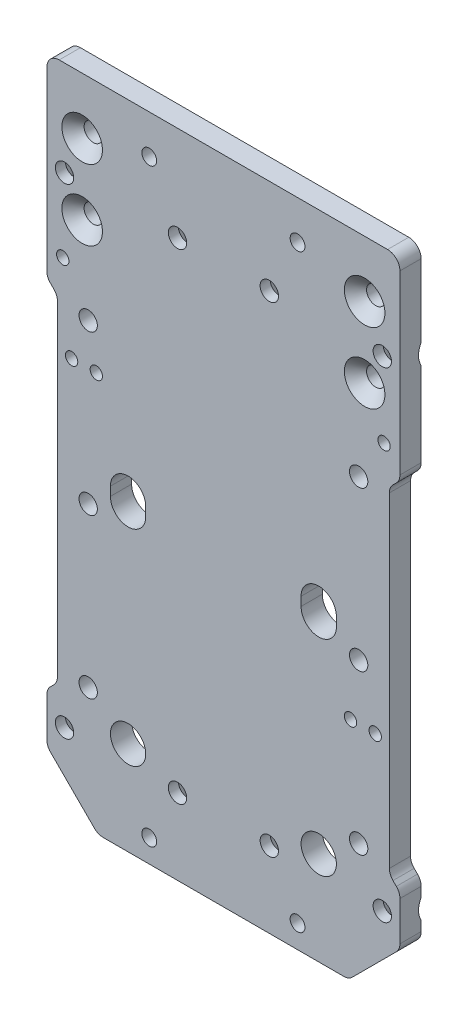
SolidWorks part; units mm, degrees
material "Polycarbonate (PC)"
ref_plane "Front Plane" through (0, 0, 0) normal (0, 0, 1) x (1, 0, 0)
ref_plane "Top Plane" through (0, 0, 0) normal (0, 1, 0) x (1, 0, 0)
ref_plane "Right Plane" through (0, 0, 0) normal (1, 0, 0) x (0, 0, -1)
sketch "Sketch1" plane through (0, 0, 0) normal (0, 0, 1) x (1, 0, 0)
  line L0 (-50, 0) -> (-35.5, -14.5)
  line L1 (-50, 0) -> (50, 0)
  line L2 (-50, 0) -> (-50, 170)
  line L3 (-50, 170) -> (50, 170)
  line L4 (50, 0) -> (50, 170)
  line L5 (-35.5, -14.5) -> (35.5, -14.5)
  line L6 (35.5, -14.5) -> (50, 0)
  line L7 (0, 0) -> (0, 178.5984) construction
  point P4 (0, 0)
  point P8 (0, -14.5)
  dimension "D1" = 100
  dimension "D3" = 14.5
  dimension "D4" = 71
  dimension "D5" = 184.5
extrude "Body" add sketch "Sketch1" along normal mid plane 6 contours L1 L4 L3 L2 | L5 L6 L1 L0 | L1 L7 L3 L2
sketch "Sketch6" plane through (0, 0, 3) normal (0, 0, 1) x (1, 0, 0)
  line L0 (-50, 115) -> (-47, 112)
  line L1 (0, 0) -> (0, 25.1631) construction
  line L2 (-47, 112) -> (-47, 17)
  line L3 (-47, 17) -> (-50, 14)
  line L4 (50, 115) -> (47, 112)
  line L5 (-35.5, -14.5) -> (35.5, -14.5) construction
  line L6 (47, 112) -> (47, 17)
  line L7 (47, 17) -> (50, 14)
  line L8 (-50, 115) -> (-50, 14)
  line L9 (50, 115) -> (50, 14)
  line L12 (-50, 0) -> (-50, 170) construction
  line L13 (50, 0) -> (50, 170) construction
  dimension "D1" = 94
  dimension "D2" = 28.5
  dimension "D3" = 45
  dimension "D4" = 129.5
extrude "ReduceSomeWidth" cut sketch "Sketch6" against normal through all
sketch "screwHeadHoleCarriageY" plane through (0, 0, -3) normal (0, 0, -1) x (-1, 0, 0)
  line L0 (0, 0) -> (0, 34.2129) construction
  line L1 (35.5, -14.5) -> (-35.5, -14.5) construction
  line L2 (-27, 70.2) -> (-27, 72.7) construction
  line L3 (-32, 70.2) -> (-32, 72.7)
  line L4 (-22, 70.2) -> (-22, 72.7)
  line L5 (27, 70.2) -> (27, 72.7) construction
  line L6 (22, 70.2) -> (22, 72.7)
  line L7 (32, 70.2) -> (32, 72.7)
  circle A0 centre (-27, 12) radius 5
  circle A1 centre (27, 12) radius 5
  arc A6 (-32, 70.2) -> (-22, 70.2) centre (-27, 70.2) ccw
  arc A7 (-22, 72.7) -> (-32, 72.7) centre (-27, 72.7) ccw
  arc A8 (22, 70.2) -> (32, 70.2) centre (27, 70.2) ccw
  arc A9 (32, 72.7) -> (22, 72.7) centre (27, 72.7) ccw
  point P18 (-27, 71.45)
  point P28 (27, 71.45)
  dimension "D3" = 10
  dimension "D5" = 12.5
  dimension "D1" = 54
  dimension "D2" = 26.5
  dimension "D4" = 84.7
extrude "CutForOtherScrewsHeads" cut sketch "screwHeadHoleCarriageY" against normal through all
fillet "EndMillMinimumRadius" radius 3.5 14 edges at (-50, 170, 0) (50, 170, 0) (47, 112, 0) (47, 17, 0) (-47, 17, 0) (-47, 112, 0) (-50, 14, 0) (-50, 0, 0) (-35.5, -14.5, 0) (50, 14, 0) (50, 0, 0) (35.5, -14.5, 0) (-50, 115, 0) (50, 115, 0)
hole_wizard "Ø3.5 (3.5) CableTieHoles" positions "Sketch9" profile "Sketch10" hole size "Ø3.5" standard "ANSI Metric" end condition through all
sketch "Sketch9" plane through (0, 0, -3) normal (0, 0, -1) x (-1, 0, 0)
  line L0 (-50, 116.4497) -> (-50, 166.5) construction
  line L1 (50, 116.4497) -> (50, 166.5) construction
  line L2 (34.0503, -14.5) -> (-34.0503, -14.5) construction
  point P0 (-45.5, 122)
  point P2 (45.5, 122)
  dimension "D1" = 4.5
  dimension "D2" = 4.5
  dimension "D3" = 136.5
sketch "Sketch10" plane through (45.5, 122, -3) normal (1, 0, 0) x (0, 1, 0)
  line L0 (0, 0) -> (0, 6)
  line L1 (0, 6) -> (1.75, 6)
  line L2 (1.75, 6) -> (1.75, 0)
  line L5 (1.75, 0) -> (0, 0)
  line L11 (0, -6.35) -> (0, 107.95) construction
  dimension "Thru Hole Dia." = 3.5
  dimension "Thru Hole Depth" = 6
hole_wizard "Ø4.2 (4.2) KP8 Holes1" positions "Sketch11" profile "Sketch12" hole size "Ø4.2" standard "ANSI Metric" end condition through all
sketch "Sketch11" plane through (0, 0, -3) normal (0, 0, -1) x (-1, 0, 0)
  line L0 (34.0503, -14.5) -> (-34.0503, -14.5) construction
  line L2 (0, 0) -> (0, 41.1682) construction
  point P0 (-21, 159)
  point P2 (21, 159)
  dimension "D1" = 42
  dimension "D2" = 173.5
sketch "Sketch12" plane through (21, 159, -3) normal (1, 0, 0) x (0, 1, 0)
  line L0 (0, 0) -> (0, 6)
  line L1 (0, 6) -> (2.1, 6)
  line L2 (2.1, 6) -> (2.1, 0)
  line L5 (2.1, 0) -> (0, 0)
  line L11 (0, -6.35) -> (0, 107.95) construction
  dimension "Thru Hole Dia." = 4.2
  dimension "Thru Hole Depth" = 6
hole_wizard "Ø4.2 (4.2) KP8 Holes2" positions "Sketch13" profile "Sketch14" hole size "Ø4.2" standard "ANSI Metric" end condition through all
sketch "Sketch13" plane through (0, 0, -3) normal (0, 0, -1) x (-1, 0, 0)
  line L0 (34.0503, -14.5) -> (-34.0503, -14.5) construction
  line L1 (0, 0) -> (0, 17.4832) construction
  point P0 (-21, -8)
  point P2 (21, -8)
  dimension "D1" = 42
  dimension "D2" = 6.5
sketch "Sketch14" plane through (21, -8, -3) normal (1, 0, 0) x (0, 1, 0)
  line L0 (0, 0) -> (0, 6)
  line L1 (0, 6) -> (2.1, 6)
  line L2 (2.1, 6) -> (2.1, 0)
  line L5 (2.1, 0) -> (0, 0)
  line L11 (0, -6.35) -> (0, 107.95) construction
  dimension "Thru Hole Dia." = 4.2
  dimension "Thru Hole Depth" = 6
hole_wizard "Ø5.2 (5.2) MountAngleCornerHoles" positions "Sketch15" profile "Sketch16" hole size "Ø5.2" standard "ANSI Metric" end condition through all
sketch "Sketch15" plane through (0, 0, -3) normal (0, 0, -1) x (-1, 0, 0)
  line L0 (0, 0) -> (0, 24.2214) construction
  line L2 (46.5, 170) -> (-46.5, 170) construction
  point P0 (-40, 154)
  point P2 (-40, 134)
  point P4 (40, 154)
  point P6 (40, 134)
  dimension "D1" = 80
  dimension "D2" = 20
  dimension "D3" = 16
sketch "Sketch16" plane through (40, 154, -3) normal (1, 0, 0) x (0, 1, 0)
  line L0 (0, 0) -> (0, 6)
  line L1 (0, 6) -> (5.75, 6)
  line L2 (2.6, 2.85) -> (2.6, 0)
  line L5 (2.6, 0) -> (0, 0)
  line L7 (5.75, 6) -> (2.6, 2.85)
  line L8 (-5.75, 6) -> (-2.6, 2.85) construction
  line L11 (0, -6.35) -> (0, 107.95) construction
  dimension "Thru Hole Dia." = 5.2
  dimension "Thru Hole Depth" = 6
  dimension "Far C'Sink Dia." = 11.5
  dimension "Far C'Sink Angle" = 90
hole_wizard "Ø5.2 (5.2) SK8 Mount Holes" positions "Sketch17" profile "Sketch20" hole size "Ø5.2" standard "ANSI Metric" end condition through all
sketch "Sketch17" plane through (0, 0, -3) normal (0, 0, -1) x (-1, 0, 0)
  line L0 (0, 0) -> (0, 35.1955) construction
  line L1 (34.0503, -14.5) -> (-34.0503, -14.5) construction
  point P0 (-45, 143.1)
  point P2 (-13, 143.1)
  point P4 (13, 143.1)
  point P6 (45, 143.1)
  point P8 (-45, 7)
  point P10 (-13, 7)
  point P12 (13, 7)
  point P14 (45, 7)
  dimension "D1" = 32
  dimension "D2" = 26
  dimension "D3" = 32
  dimension "D4" = 21.5
  dimension "D5" = 157.6
sketch "Sketch20" plane through (45, 143.1, -3) normal (1, 0, 0) x (0, 1, 0)
  line L0 (0, 0) -> (0, 6)
  line L1 (0, 6) -> (2.6, 6)
  line L2 (2.6, 6) -> (2.6, 3.15)
  line L3 (2.6, 3.15) -> (5.75, 0)
  line L5 (5.75, 0) -> (0, 0)
  line L6 (-2.6, 3.15) -> (-5.75, 0) construction
  line L11 (0, -6.35) -> (0, 107.95) construction
  dimension "Thru Hole Dia." = 5.2
  dimension "Thru Hole Depth" = 6
  dimension "Near C'Sink Dia." = 11.5
  dimension "Near C'Sink Angle" = 90
hole_wizard "Ø3.5 (3.5) EndSensorsHoles" positions "Sketch21" profile "Sketch22" hole size "Ø3.5" standard "ANSI Metric" end condition through all
sketch "Sketch21" plane through (0, 0, -3) normal (0, 0, -1) x (-1, 0, 0)
  line L2 (34.0503, -14.5) -> (-34.0503, -14.5) construction
  point P0 (-43, 49.5)
  point P2 (-36, 49.5)
  point P4 (36, 98.5)
  point P6 (43, 98.5)
  dimension "D1" = 7
  dimension "D2" = 7
  dimension "D3" = 72
  dimension "D4" = 64
  dimension "D5" = 113
sketch "Sketch22" plane through (43, 49.5, -3) normal (1, 0, 0) x (0, 1, 0)
  line L0 (0, 0) -> (0, 6)
  line L1 (0, 6) -> (1.75, 6)
  line L2 (1.75, 6) -> (1.75, 1.5)
  line L3 (1.75, 1.5) -> (3.25, 0)
  line L5 (3.25, 0) -> (0, 0)
  line L6 (-1.75, 1.5) -> (-3.25, 0) construction
  line L11 (0, -6.35) -> (0, 107.95) construction
  dimension "Thru Hole Dia." = 3.5
  dimension "Thru Hole Depth" = 6
  dimension "Near C'Sink Dia." = 6.5
  dimension "Near C'Sink Angle" = 90
hole_wizard "Ø5.2 (5.2) MountToBaseHoles" positions "Sketch23" profile "Sketch24" hole size "Ø5.2" standard "ANSI Metric" end condition through all
sketch "Sketch23" plane through (0, 0, 3) normal (0, 0, 1) x (1, 0, 0)
  line L0 (0, 0) -> (0, 21.7136) construction
  line L3 (-34.0503, -14.5) -> (34.0503, -14.5) construction
  point P0 (-38.3, 110.2)
  point P2 (-38.3, 65.2)
  point P4 (-38.3, 20.2)
  point P6 (38.3, 20.2)
  point P8 (38.3, 65.2)
  point P10 (38.3, 110.2)
  dimension "D1" = 76.6
  dimension "D2" = 34.7
  dimension "D3" = 124.7
  dimension "D4" = 79.7
sketch "Sketch24" plane through (-38.3, 110.2, 3) normal (1, 0, 0) x (0, -1, 0)
  line L0 (0, 0) -> (0, 6)
  line L1 (0, 6) -> (2.6, 6)
  line L2 (2.6, 6) -> (2.6, 0)
  line L5 (2.6, 0) -> (0, 0)
  line L11 (0, -6.35) -> (0, 107.95) construction
  dimension "Thru Hole Dia." = 5.2
  dimension "Thru Hole Depth" = 6
